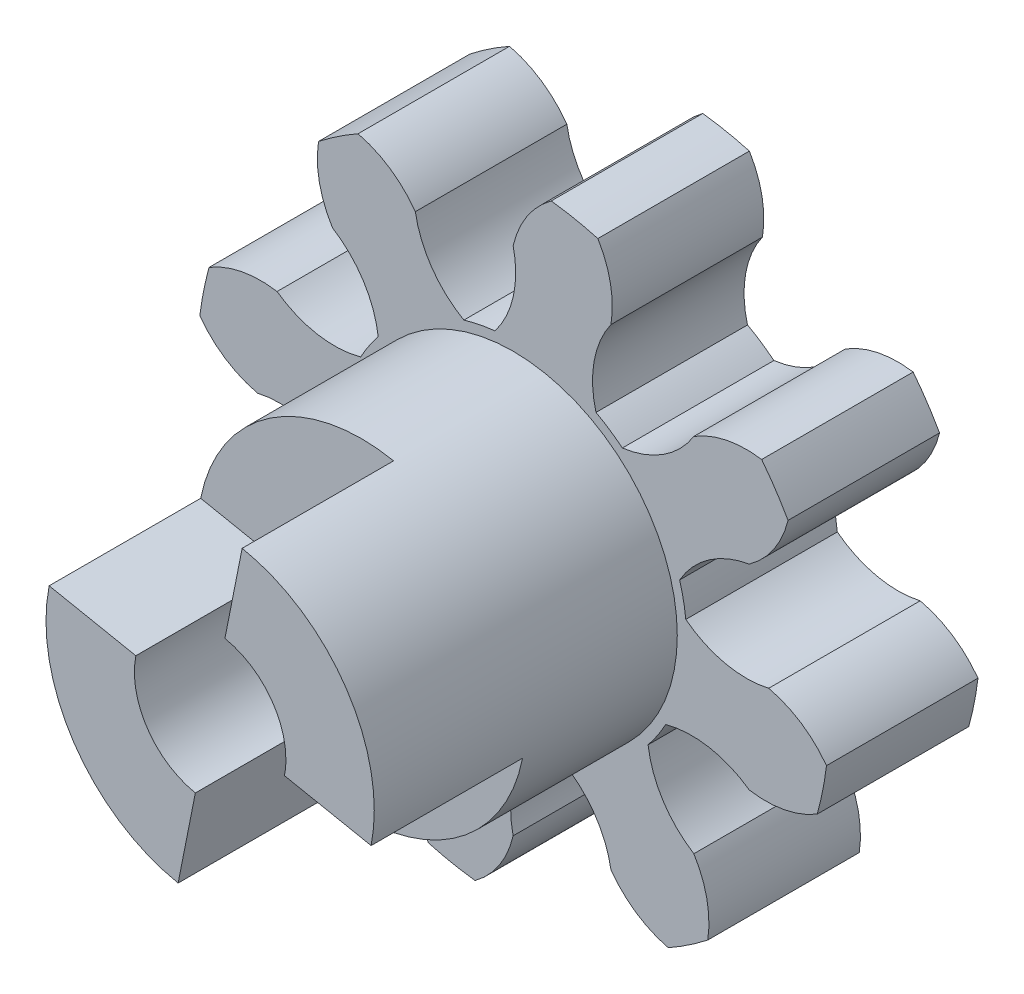
SolidWorks part; units mm, degrees
ref_plane "Alzado" through (0, 0, 0) normal (0, 0, 1) x (1, 0, 0)
ref_plane "Planta" through (0, 0, 0) normal (0, 1, 0) x (1, 0, 0)
ref_plane "Vista lateral" through (0, 0, 0) normal (1, 0, 0) x (0, 0, -1)
sketch "Croquis1" plane through (0, 0, 0) normal (0, 0, 1) x (1, 0, 0)
  arc A0 (3.4186, 0.3599) -> (5.06, 0) centre (4.6194, 1.9134) ccw
  arc A1 (6.2043, -0.7544) -> (5.06, 0) centre (4.6194, -1.9134) ccw
  arc A2 (4.6748, -1.9364) -> (6.0207, -1.6773) centre (5, 0) ccw
  arc A3 (6.0207, -1.6773) -> (6.2043, -0.7544) centre (0, 0) ccw
  arc A4 (4.6748, -1.9364) -> (3.0207, -1.6407) centre (3.5355, -3.5355) ccw
  arc A5 (2.6718, -2.1628) -> (3.0207, -1.6407) centre (0, 0) ccw
  arc A6 (4.9205, 3.8537) -> (3.578, 3.578) centre (4.6194, 1.9134) ccw
  arc A7 (4.6748, 1.9364) -> (3.2961, 0.9757) centre (5, 0) ccw
  arc A8 (2.6718, -2.1628) -> (3.578, -3.578) centre (4.6194, -1.9134) ccw
  arc A9 (3.8537, -4.9205) -> (3.578, -3.578) centre (1.9134, -4.6194) ccw
  arc A10 (1.9364, -4.6748) -> (3.0712, -5.4433) centre (3.5355, -3.5355) ccw
  arc A11 (3.0712, -5.4433) -> (3.8537, -4.9205) centre (0, 0) ccw
  arc A12 (1.9364, -4.6748) -> (0.9757, -3.2961) centre (0, -5) ccw
  arc A13 (0.3599, -3.4186) -> (0.9757, -3.2961) centre (0, 0) ccw
  arc A14 (0.3599, -3.4186) -> (0, -5.06) centre (1.9134, -4.6194) ccw
  arc A15 (-0.7544, -6.2043) -> (0, -5.06) centre (-1.9134, -4.6194) ccw
  arc A16 (-1.9364, -4.6748) -> (-1.6773, -6.0207) centre (0, -5) ccw
  arc A17 (-1.6773, -6.0207) -> (-0.7544, -6.2043) centre (0, 0) ccw
  arc A18 (-1.9364, -4.6748) -> (-1.6407, -3.0207) centre (-3.5355, -3.5355) ccw
  arc A19 (-2.1628, -2.6718) -> (-1.6407, -3.0207) centre (0, 0) ccw
  arc A20 (5.4433, 3.0712) -> (4.9205, 3.8537) centre (0, 0) ccw
  arc A21 (2.1628, 2.6718) -> (3.578, 3.578) centre (1.9134, 4.6194) ccw
  arc A22 (4.6748, 1.9364) -> (5.4433, 3.0712) centre (3.5355, 3.5355) ccw
  arc A23 (-2.1628, -2.6718) -> (-3.578, -3.578) centre (-1.9134, -4.6194) ccw
  arc A24 (-4.9205, -3.8537) -> (-3.578, -3.578) centre (-4.6194, -1.9134) ccw
  arc A25 (-4.6748, -1.9364) -> (-5.4433, -3.0712) centre (-3.5355, -3.5355) ccw
  arc A26 (-5.4433, -3.0712) -> (-4.9205, -3.8537) centre (0, 0) ccw
  arc A27 (-4.6748, -1.9364) -> (-3.2961, -0.9757) centre (-5, 0) ccw
  arc A28 (-3.4186, -0.3599) -> (-3.2961, -0.9757) centre (0, 0) ccw
  arc A29 (-3.4186, -0.3599) -> (-5.06, 0) centre (-4.6194, -1.9134) ccw
  arc A30 (-6.2043, 0.7544) -> (-5.06, 0) centre (-4.6194, 1.9134) ccw
  arc A31 (-4.6748, 1.9364) -> (-6.0207, 1.6773) centre (-5, 0) ccw
  arc A33 (-6.0207, 1.6773) -> (-6.2043, 0.7544) centre (0, 0) ccw
  arc A34 (-4.6748, 1.9364) -> (-3.0207, 1.6407) centre (-3.5355, 3.5355) ccw
  arc A35 (-2.6718, 2.1628) -> (-3.0207, 1.6407) centre (0, 0) ccw
  arc A36 (-2.6718, 2.1628) -> (-3.578, 3.578) centre (-4.6194, 1.9134) ccw
  arc A37 (-3.8537, 4.9205) -> (-3.578, 3.578) centre (-1.9134, 4.6194) ccw
  arc A38 (-1.9364, 4.6748) -> (-3.0712, 5.4433) centre (-3.5355, 3.5355) ccw
  arc A39 (-3.0712, 5.4433) -> (-3.8537, 4.9205) centre (0, 0) ccw
  arc A40 (-1.9364, 4.6748) -> (-0.9757, 3.2961) centre (0, 5) ccw
  arc A41 (-0.3599, 3.4186) -> (-0.9757, 3.2961) centre (0, 0) ccw
  arc A42 (-0.3599, 3.4186) -> (0, 5.06) centre (-1.9134, 4.6194) ccw
  arc A43 (0.7544, 6.2043) -> (0, 5.06) centre (1.9134, 4.6194) ccw
  arc A44 (1.9364, 4.6748) -> (1.6773, 6.0207) centre (0, 5) ccw
  arc A45 (1.6773, 6.0207) -> (0.7544, 6.2043) centre (0, 0) ccw
  arc A46 (1.9364, 4.6748) -> (1.6407, 3.0207) centre (3.5355, 3.5355) ccw
  arc A47 (2.1628, 2.6718) -> (1.6407, 3.0207) centre (0, 0) ccw
  arc A51 (3.4186, 0.3599) -> (3.2961, 0.9757) centre (0, 0) ccw
  point P96 (0, 0)
  dimension "D1" = 8
extrude "Saliente-Extruir1" add sketch "Croquis1" along normal blind 3
sketch "Croquis2" plane through (0, 0, 3) normal (0, 0, 1) x (1, 0, 0)
  circle A0 centre (0, 0) radius 3.25
  dimension "D1" = 6.5
extrude "Saliente-Extruir2" add sketch "Croquis2" along normal blind 3
sketch "Croquis3" plane through (0, 0, 6) normal (0, 0, 1) x (1, 0, 0)
  circle A0 centre (0, 0) radius 3.25
  dimension "D1" = 6.5
extrude "Saliente-Extruir3" add sketch "Croquis3" along normal blind 3
sketch "Croquis4" plane through (0, 0, 9) normal (0, 0, 1) x (1, 0, 0)
  line L0 (1.2193, 6.1299) -> (-1.2193, -6.1299)
  line L1 (-6.1299, 1.2193) -> (6.1299, -1.2193)
  line L2 (-6.1299, 1.2193) -> (1.2193, 6.1299)
  line L3 (-1.2193, -6.1299) -> (6.1299, -1.2193)
  arc A0 (1.6773, 6.0207) -> (0.7544, 6.2043) centre (0, 0) ccw construction
  arc A1 (-1.6773, -6.0207) -> (-0.7544, -6.2043) centre (0, 0) ccw construction
  arc A2 (-6.0207, 1.6773) -> (-6.2043, 0.7544) centre (0, 0) ccw construction
  arc A3 (6.0207, -1.6773) -> (6.2043, -0.7544) centre (0, 0) ccw construction
  circle A4 centre (0, 0) radius 1.5
  circle M1 centre (0, 0) radius 3.25
  dimension "D1" = 3
extrude "Cortar-Extruir2" cut sketch "Croquis4" against normal blind 3 contours A4 L0 L1 M1 | L0 A4 L1 | L1 A4 L0 | L0 A4 L1 | L1 A4 L0 | A4 L0 L1 M1
sketch "Croquis5" plane through (0, 0, 3) normal (0, 0, 1) x (1, 0, 0)
  line L0 (0.4877, 2.452) -> (1.2193, 6.1299)
sketch "Croquis6" plane through (0, 0, 6) normal (0, 0, 1) x (1, 0, 0)
  circle A0 centre (0, 0) radius 1.5
extrude "Cortar-Extruir3" cut sketch "Croquis6" against normal blind 10
